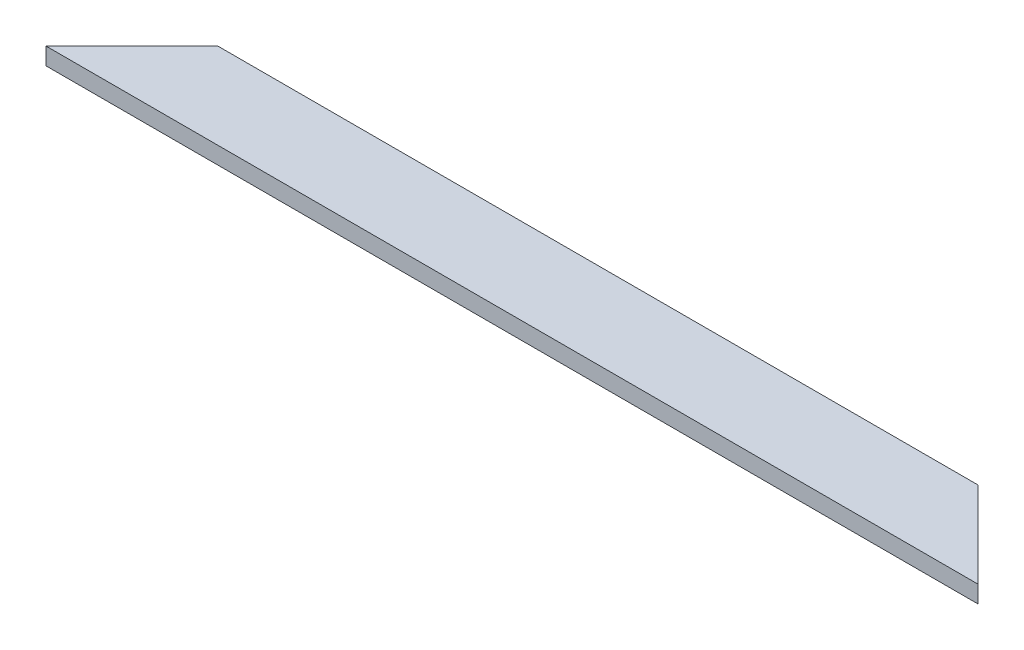
SolidWorks part; units mm, degrees
ref_plane "Спереди" through (0, 0, 0) normal (0, 0, 1) x (1, 0, 0)
ref_plane "Сверху" through (0, 0, 0) normal (0, 1, 0) x (1, 0, 0)
ref_plane "Справа" through (0, 0, 0) normal (1, 0, 0) x (0, 0, -1)
sketch "Эскиз1" plane through (0, 0, 0) normal (1, 0, 0) x (0, 0, -1)
  line L1 (0, 0) -> (20, 0)
  line L2 (0, 0) -> (0, 4)
  line L3 (0, 4) -> (20, 4)
  line L4 (20, 0) -> (20, 4)
extrude "Бобышка-Вытянуть1" add sketch "Эскиз1" along normal blind 217
sketch "Эскиз2" plane through (0, 4, 0) normal (0, 1, 0) x (1, 0, 0)
  line L0 (0, 0) -> (20, 20)
  line L1 (217, 20) -> (0, 20) construction
  line L2 (20, 20) -> (197, 20)
  line L3 (197, 20) -> (217, 0)
  line L4 (217, 0) -> (0, 0)
extrude "Вырез-Вытянуть1" cut sketch "Эскиз2" against normal blind 10 flip side to cut
